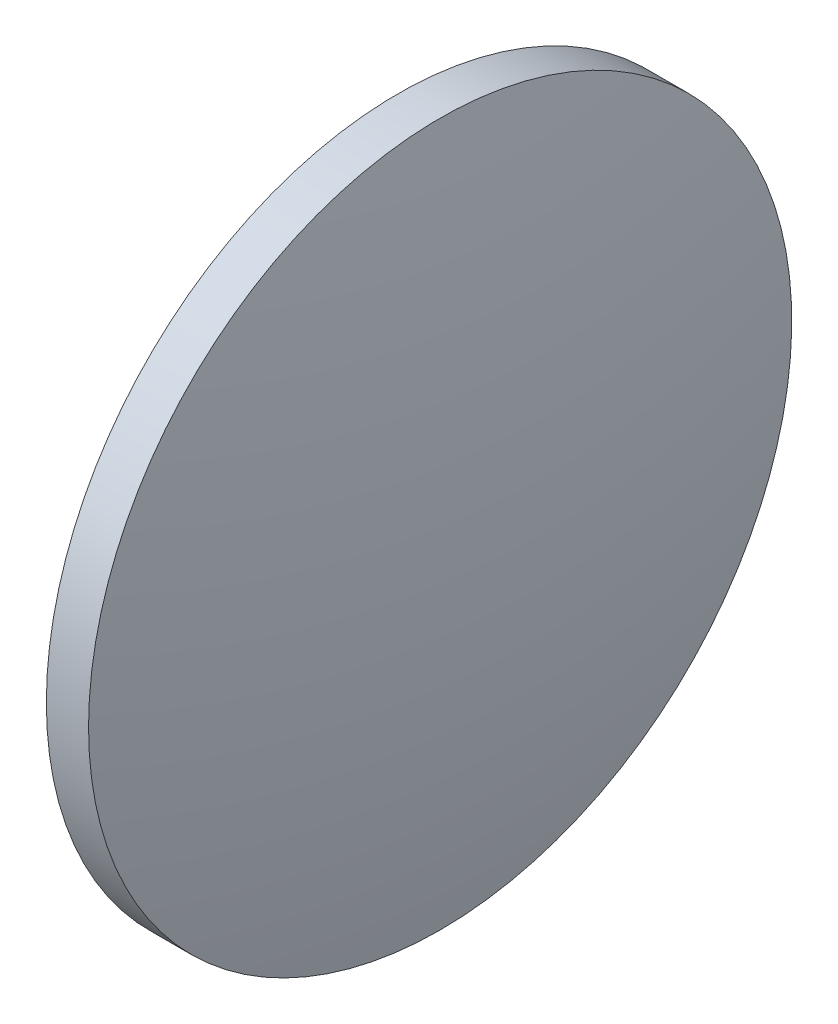
SolidWorks part; units mm, degrees
ref_plane "前视基准面" through (0, 0, 0) normal (0, 0, 1) x (1, 0, 0)
ref_plane "上视基准面" through (0, 0, 0) normal (0, 1, 0) x (1, 0, 0)
ref_plane "右视基准面" through (0, 0, 0) normal (1, 0, 0) x (0, 0, -1)
sketch "草图1" plane through (0, 0, 0) normal (0, 0, 1) x (1, 0, 0)
  line L0 (448.1262, -45.5784) -> (468.4147, -45.5784) construction
  line L1 (452.2712, -45.5784) -> (452.2712, -20.5784)
  line L2 (452.2712, -20.5784) -> (455.2712, -20.5784)
  line L3 (457.7112, -45.5784) -> (452.2712, -45.5784)
  arc A0 (457.7112, -45.5784) -> (455.2712, -20.5784) centre (328.4174, -45.5784) ccw
revolve "旋转1" add sketch "草图1" angle 360 about L0
